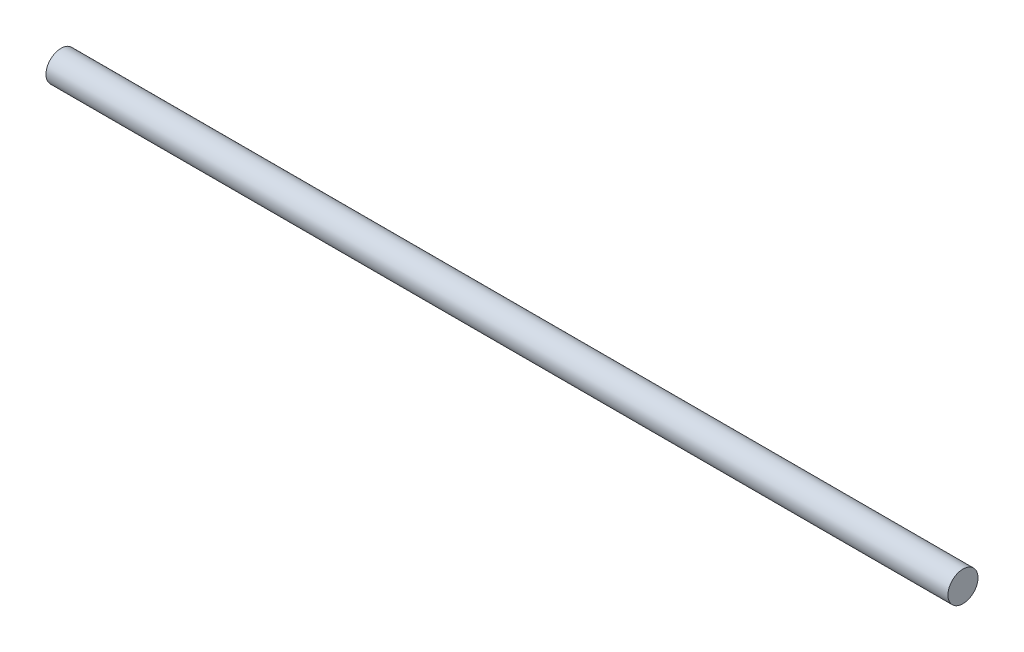
SolidWorks part; units mm, degrees
ref_plane "Front Plane" through (0, 0, 0) normal (0, 0, 1) x (1, 0, 0)
ref_plane "Top Plane" through (0, 0, 0) normal (0, 1, 0) x (1, 0, 0)
ref_plane "Right Plane" through (0, 0, 0) normal (1, 0, 0) x (0, 0, -1)
sketch "Sketch1" plane through (0, 0, 0) normal (1, 0, 0) x (0, 0, -1)
  circle A0 centre (0, 0) radius 5
extrude "Boss-Extrude1" add sketch "Sketch1" along normal blind 300
